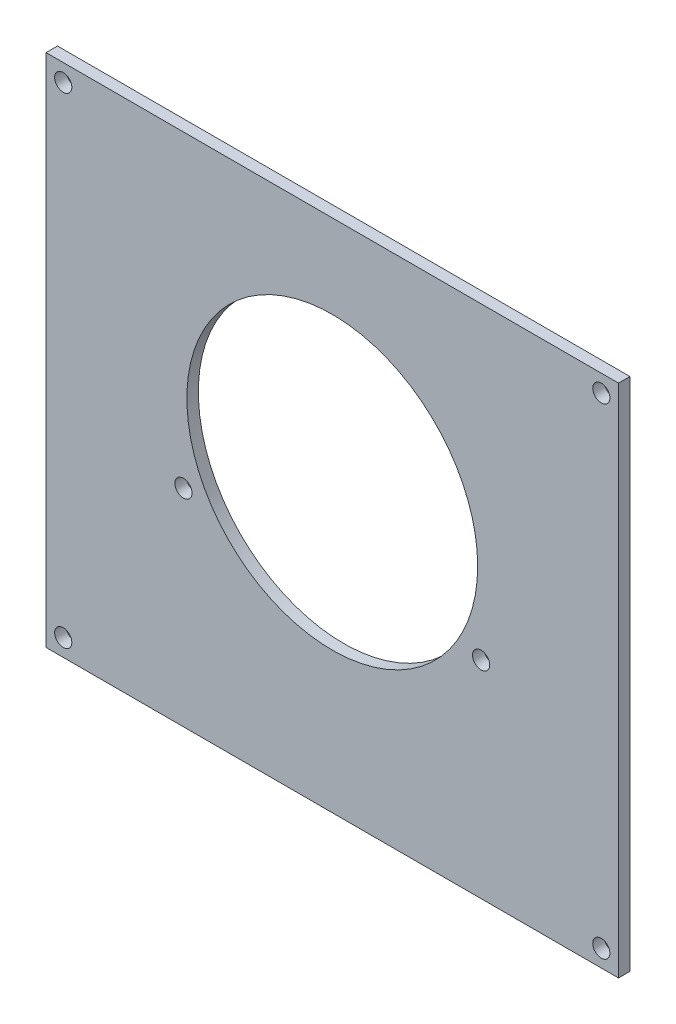
SolidWorks part; units mm, degrees
ref_plane "Front Plane" through (0, 0, 0) normal (0, 0, 1) x (1, 0, 0)
ref_plane "Top Plane" through (0, 0, 0) normal (0, 1, 0) x (1, 0, 0)
ref_plane "Right Plane" through (0, 0, 0) normal (1, 0, 0) x (0, 0, -1)
sketch "Sketch1" plane through (0, 0, 0) normal (0, 0, 1) x (1, 0, 0)
  line L1 (-76.2247, 86.3144) -> (23.7753, 86.3144)
  line L2 (-76.2247, 86.3144) -> (-76.2247, -3.6856)
  line L3 (-76.2247, -3.6856) -> (23.7753, -3.6856)
  line L4 (23.7753, 86.3144) -> (23.7753, -3.6856)
  dimension "D1" = 100
  dimension "D2" = 90
extrude "Boss-Extrude1" add sketch "Sketch1" along normal blind 2
sketch "Sketch2" plane through (0, 0, 2) normal (0, 0, 1) x (1, 0, 0)
  line L0 (-26.2247, -915.8612) -> (-26.2247, 49084.1388) construction
  line L1 (23.7753, 86.3144) -> (-76.2247, 86.3144) construction
  circle A0 centre (-26.2247, 46.3144) radius 25.4
  point P5 (-26.2247, 86.3144)
  dimension "D1" = 40
extrude "Cut-Extrude1" cut sketch "Sketch2" against normal blind 3
sketch "Sketch3" plane through (0, 0, 2) normal (0, 0, 1) x (1, 0, 0)
  line L0 (-26.2247, -915.8612) -> (-26.2247, 49084.1388) construction
  line L1 (23.7753, 86.3144) -> (-76.2247, 86.3144) construction
  circle A0 centre (-52.2247, 32.4144) radius 1.5
  circle A1 centre (-0.2247, 32.4144) radius 1.5
  circle A2 centre (-26.2247, 46.3144) radius 25.4 construction
  point P11 (-26.2247, 86.3144)
  dimension "D1" = 13.9
  dimension "D2" = 13.9
  dimension "D5" = 3
  dimension "D6" = 3
  dimension "D3" = 52
  dimension "D4" = 26
extrude "Cut-Extrude2" cut sketch "Sketch3" against normal blind 3
sketch "Sketch4" plane through (0, 0, 0) normal (0, 0, -1) x (-1, 0, 0)
  line L0 (-23.7753, 86.3144) -> (76.2247, 86.3144) construction
  line L1 (-23.7753, -3.6856) -> (-23.7753, 86.3144) construction
  line L2 (76.2247, 86.3144) -> (76.2247, -3.6856) construction
  line L3 (76.2247, -3.6856) -> (-23.7753, -3.6856) construction
  circle A0 centre (-20.7753, 83.3144) radius 1.5
  circle A1 centre (73.2247, 83.3144) radius 1.5
  circle A2 centre (73.2247, -0.6856) radius 1.5
  circle A3 centre (-20.7753, -0.6856) radius 1.5
  dimension "D1" = 3
  dimension "D2" = 3
  dimension "D3" = 3
  dimension "D4" = 3
  dimension "D5" = 3
  dimension "D7" = 3
  dimension "D8" = 3
  dimension "D9" = 3
  dimension "D10" = 3
  dimension "D12" = 3
  dimension "D6" = 3
  dimension "D11" = 3
extrude "Cut-Extrude3" cut sketch "Sketch4" against normal blind 10
hole_wizard "CSK for #0 Flat Head Machine Screw (100)2" positions "Sketch7" profile "Sketch8" countersink size "#0" standard "ANSI Inch" end condition through all
sketch "Sketch7" plane through (0, 0, 0) normal (0, 0, -1) x (-1, 0, 0)
  point P0 (-20.7753, 83.3144)
  point P3 (73.2247, 83.3144)
  point P6 (73.2247, -0.6856)
  point P9 (-20.7753, -0.6856)
sketch "Sketch8" plane through (20.7753, 83.3144, 0) normal (1, 0, 0) x (0, 1, 0)
  line L0 (0, 0) -> (0, 2)
  line L1 (0, 2) -> (0.889, 2)
  line L2 (0.889, 2) -> (0.889, 0.5222)
  line L3 (0.889, 0.5222) -> (1.5113, 0)
  line L5 (1.5113, 0) -> (0, 0)
  line L6 (-0.889, 0.5222) -> (-1.5113, 0) construction
  line L11 (0, -6.35) -> (0, 107.95) construction
  dimension "Thru Hole Dia." = 1.778
  dimension "Thru Hole Depth" = 2
  dimension "Near C'Sink Dia." = 3.0226
  dimension "Near C'Sink Angle" = 100
